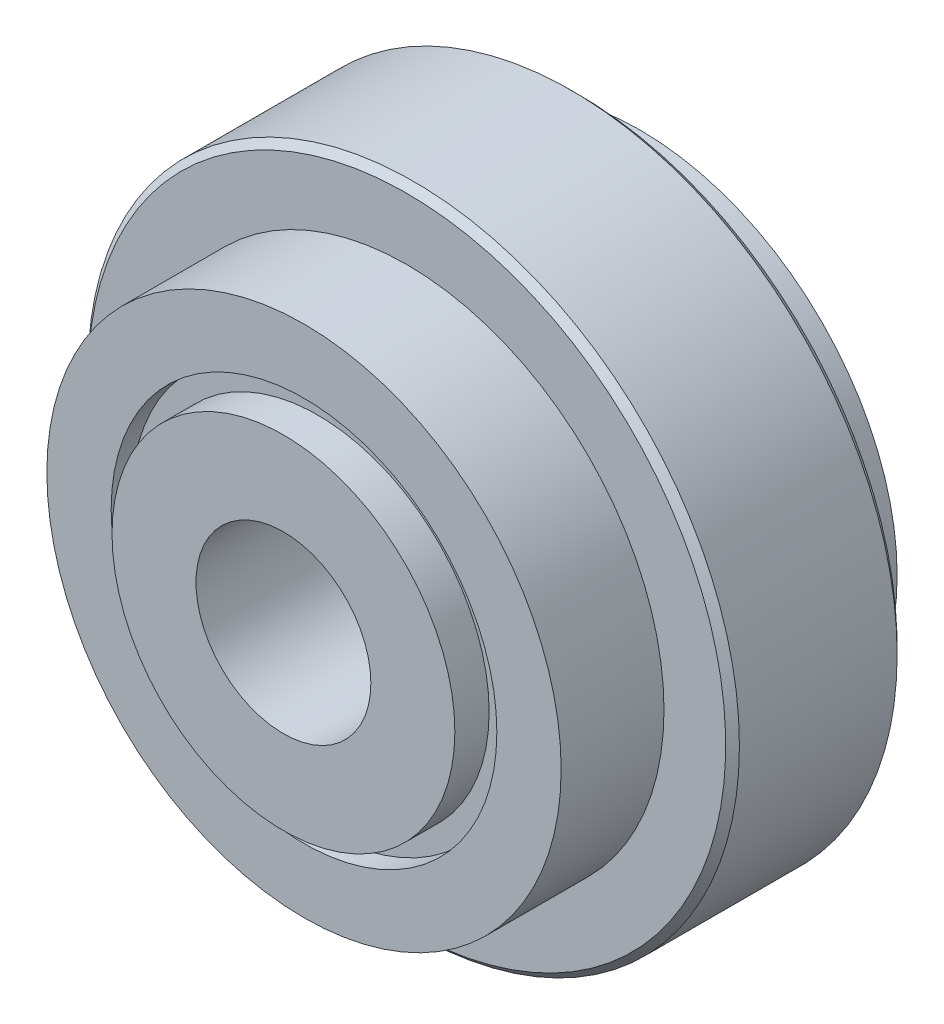
SolidWorks part; units mm, degrees
ref_plane "Front Plane" through (0, 0, 0) normal (0, 0, 1) x (1, 0, 0)
ref_plane "Top Plane" through (0, 0, 0) normal (0, 1, 0) x (1, 0, 0)
ref_plane "Right Plane" through (0, 0, 0) normal (1, 0, 0) x (0, 0, -1)
sketch "Sketch1" plane through (0, 0, 0) normal (1, 0, 0) x (0, 0, -1)
  line L0 (-3.8, 3.55) -> (3.8, 3.55)
  line L1 (-4.9, 5.625) -> (-4.9, 7.5)
  line L2 (4.9, 5.625) -> (4.9, 7.5)
  line L3 (-4.9, 7.5) -> (-1.9, 7.5)
  line L4 (-1.9, 7.5) -> (-1.9, 9.3)
  line L5 (-1.9, 9.3) -> (-1.7, 9.5)
  line L6 (3.1, 9.3) -> (3.1, 7.5)
  line L7 (3.1, 7.5) -> (4.9, 7.5)
  line L8 (2.9, 9.5) -> (3.1, 9.3)
  line L10 (-1.7, 9.5) -> (2.9, 9.5)
  line L11 (4.9, 0) -> (-4.9, 0) construction
  line L13 (-4.9, 5.625) -> (-4.3, 5.625)
  line L14 (-4.3, 5.625) -> (-4.3, 4.05)
  line L15 (4.3, 4.05) -> (4.3, 5.625)
  line L16 (4.3, 5.625) -> (4.9, 5.625)
  arc A0 (-4.3, 4.05) -> (-3.8, 3.55) centre (-3.8, 4.05) ccw
  arc A1 (4.3, 4.05) -> (3.8, 3.55) centre (3.8, 4.05) cw
  point P6 (-4.3, 3.55)
  point P14 (4.3, 3.55)
  dimension "D10" = 45
  dimension "D13" = 0.5
  dimension "D14" = 0.5
  dimension "D1" = 7.1
  dimension "D2" = 9.8
  dimension "D3" = 19
  dimension "D4" = 15
  dimension "D5" = 15
  dimension "D6" = 5
  dimension "D7" = 3
  dimension "D8" = 1.8
  dimension "D9" = 0.2
  dimension "D11" = 0.2
  dimension "D12" = 45
  dimension "D19" = 8.6
  dimension "D20" = 0.6
  dimension "D21" = 0.6
  dimension "D22" = 11.25
  dimension "D23" = 11.25
revolve "Revolve1" add sketch "Sketch1" angle 360 mid plane about L11
sketch "Sketch2" plane through (0, 0, 0) normal (1, 0, 0) x (0, 0, -1)
  line L0 (-4.9, 0) -> (4.9, 0) construction
  line L1 (-5.5, 5) -> (-4.5, 5)
  line L2 (-5.5, 5) -> (-5.5, 2.55)
  line L3 (-5.5, 2.55) -> (4.5, 2.55)
  line L4 (4.5, 3.5) -> (4.5, 2.55)
  line L5 (0, 0) -> (0, 3.5) construction
  line L6 (-4.5, 5) -> (-4.5, 3.5)
  line L7 (-4.5, 3.5) -> (4.5, 3.5)
  dimension "D1" = 10
  dimension "D2" = 5.1
  dimension "D3" = 9
  dimension "D4" = 7
  dimension "D5" = 1
revolve "Revolve2" add sketch "Sketch2" angle 360 about L0
sketch "Sketch3" plane through (0, 0, 0) normal (1, 0, 0) x (0, 0, -1)
  line L0 (-4.9, 0) -> (4.9, 0) construction
  line L1 (4.5, 5) -> (5.5, 5)
  line L2 (4.5, 5) -> (4.5, 2.75)
  line L3 (4.5, 2.75) -> (5.5, 2.75)
  line L4 (5.5, 5) -> (5.5, 2.75)
  line L5 (4.5, 3.5) -> (4.5, 2.55) construction
  dimension "D1" = 10
  dimension "D2" = 5.5
  dimension "D3" = 1
revolve "Revolve3" add sketch "Sketch3" angle 360 mid plane about L0
